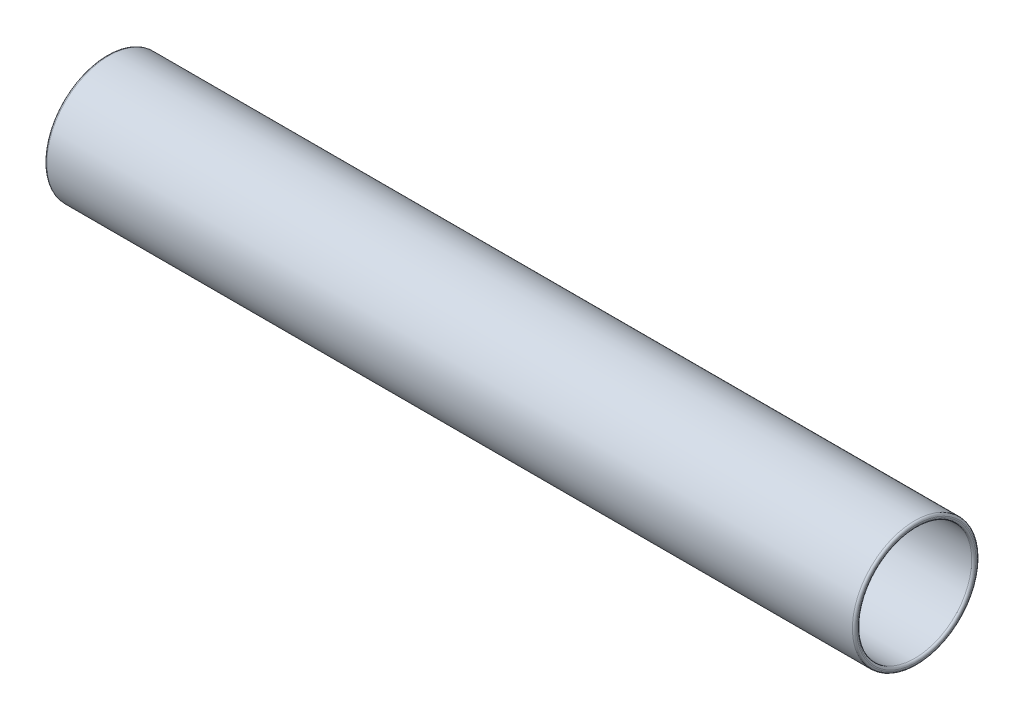
SolidWorks part; units mm, degrees
ref_plane "Front Plane" through (0, 0, 0) normal (0, 0, 1) x (1, 0, 0)
ref_plane "Top Plane" through (0, 0, 0) normal (0, 1, 0) x (1, 0, 0)
ref_plane "Right Plane" through (0, 0, 0) normal (1, 0, 0) x (0, 0, -1)
sketch "Sketch1" plane through (0, 0, 0) normal (1, 0, 0) x (0, 0, -1)
  circle A0 centre (0, 0) radius 57.75
  circle A1 centre (0, 0) radius 52.75
  circle A2 centre (0, 0) radius 66.25 construction
  dimension "D1" = 115.5
  dimension "D2" = 5
extrude "Boss-Extrude1" add sketch "Sketch1" along normal blind 750
fillet "Fillet1" radius 2 2 edges at (750, 0, -52.75) (750, 0, -57.75)
fillet "Fillet2" radius 2 2 edges at (0, 0, -52.75) (0, 0, -57.75)
